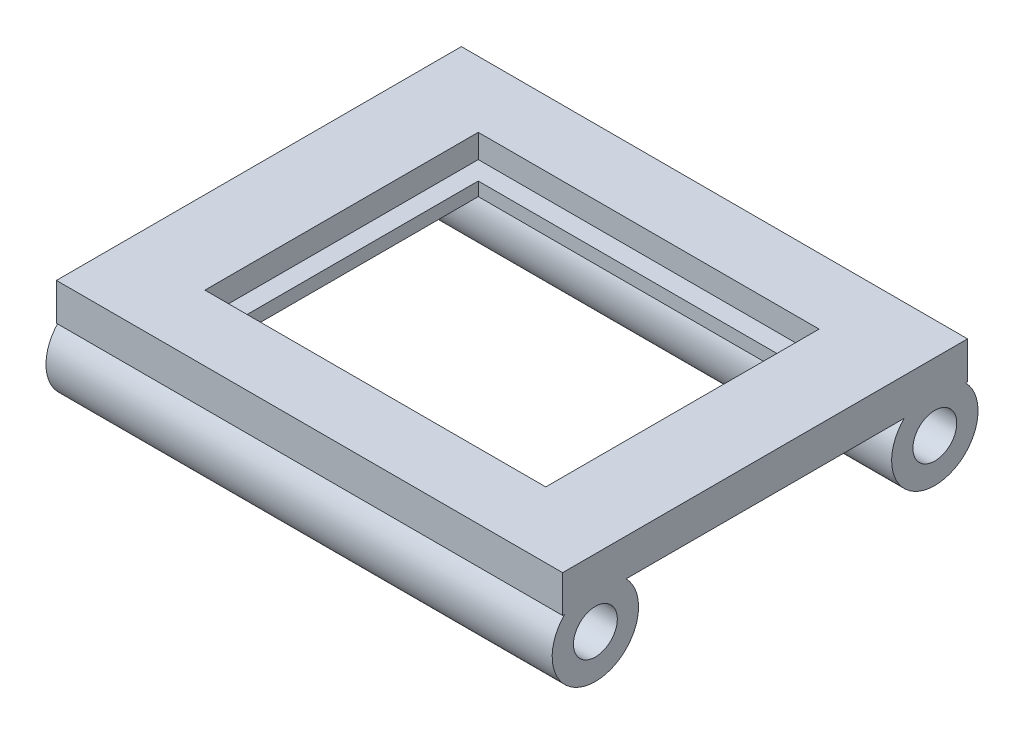
SolidWorks part; units mm, degrees
ref_plane "Front Plane" through (0, 0, 0) normal (0, 0, 1) x (1, 0, 0)
ref_plane "Top Plane" through (0, 0, 0) normal (0, 1, 0) x (1, 0, 0)
ref_plane "Right Plane" through (0, 0, 0) normal (1, 0, 0) x (0, 0, -1)
sketch "Sketch3" plane through (0, 0, 0) normal (0, 1, 0) x (1, 0, 0)
  line L1 (-75, 60) -> (75, 60)
  line L2 (-75, 60) -> (-75, -60)
  line L3 (-75, -60) -> (75, -60)
  line L4 (75, 60) -> (75, -60)
  line L5 (-75, 60) -> (75, -60) construction
  line L6 (-75, -60) -> (75, 60) construction
  point P0 (0, 0)
  dimension "D1" = 150
  dimension "D2" = 120
extrude "Boss-Extrude1" add sketch "Sketch3" along normal blind 11
sketch "Sketch4" plane through (0, 11, 0) normal (0, 1, 0) x (1, 0, 0)
  line L1 (-50.5, 40.5) -> (50.5, 40.5)
  line L2 (-50.5, 40.5) -> (-50.5, -40.5)
  line L3 (-50.5, -40.5) -> (50.5, -40.5)
  line L4 (50.5, 40.5) -> (50.5, -40.5)
  line L5 (-50.5, 40.5) -> (50.5, -40.5) construction
  line L6 (-50.5, -40.5) -> (50.5, 40.5) construction
  point P0 (0, 0)
  dimension "D1" = 101
  dimension "D2" = 81
extrude "Cut-Extrude1" cut sketch "Sketch4" against normal blind 7
sketch "Sketch5" plane through (0, 4, 0) normal (0, 1, 0) x (1, 0, 0)
  line L1 (-45, 35) -> (45, 35)
  line L2 (-45, 35) -> (-45, -35)
  line L3 (-45, -35) -> (45, -35)
  line L4 (45, 35) -> (45, -35)
  line L5 (-45, 35) -> (45, -35) construction
  line L6 (-45, -35) -> (45, 35) construction
  point P0 (0, 0)
  dimension "D1" = 90
  dimension "D2" = 70
extrude "Cut-Extrude2" cut sketch "Sketch5" against normal through all
sketch "Sketch7" plane through (-75, 0, 0) normal (-1, 0, 0) x (0, 0, 1)
  line L0 (-60, 0) -> (60, 0) construction
  line L1 (41.1944, 0) -> (59.3976, 0)
  arc A0 (41.1944, 0) -> (59.3976, 0) centre (50.296, -9) ccw
  circle A1 centre (50.296, -9) radius 6.5
  dimension "D1" = 25.6
  dimension "D4" = 13
  dimension "D2" = 50.296
  dimension "D3" = 9
extrude "Boss-Extrude2" add sketch "Sketch7" against normal up to surface (150 mm away) up to face at (75, 5.5, 0)
mirror "Mirror1" about plane through (0, 0, 0) normal (0, 0, 1) of "Boss-Extrude2"
